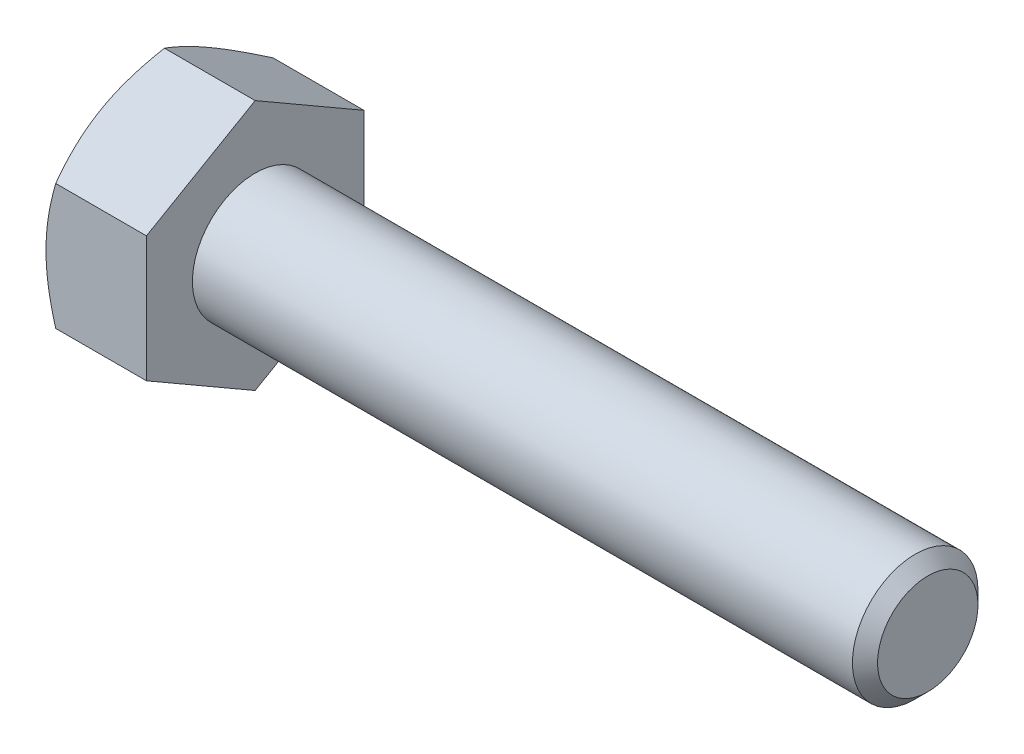
SolidWorks part; units mm, degrees
ref_plane "Front Plane" through (0, 0, 0) normal (0, 0, 1) x (1, 0, 0)
ref_plane "Top Plane" through (0, 0, 0) normal (0, 1, 0) x (1, 0, 0)
ref_plane "Right Plane" through (0, 0, 0) normal (1, 0, 0) x (0, 0, -1)
sketch "Sketch1" plane through (0, 0, 0) normal (1, 0, 0) x (0, 0, -1)
  line L1 (0, 28) -> (-24.2487, 14)
  line L2 (-24.2487, 14) -> (-24.2487, -14)
  line L3 (-24.2487, -14) -> (0, -28)
  line L4 (0, -28) -> (24.2487, -14)
  line L5 (24.2487, -14) -> (24.2487, 14)
  line L6 (24.2487, 14) -> (0, 28)
  dimension "D1" = 28
extrude "Boss-Extrude1" add sketch "Sketch1" against normal blind 22.4
sketch "Sketch2" plane through (0, 0, 0) normal (1, 0, 0) x (0, 0, -1)
  circle A0 centre (0, 0) radius 14
extrude "Boss-Extrude2" add sketch "Sketch2" along normal blind 150
cosmetic thread "Cosmetic Thread1" parameters "D1"=60, "D2"=23.704
chamfer "Chamfer1" distance 2.8 angle 45 1 edges at (150, 0, -14)
sketch "Sketch3" plane through (-22.4, 0, 0) normal (-1, 0, 0) x (0, 0, 1)
  circle A0 centre (0, 0) radius 24.2487
extrude "Cut-Extrude1" cut sketch "Sketch3" against normal blind 150 draft 60 flip side to cut
